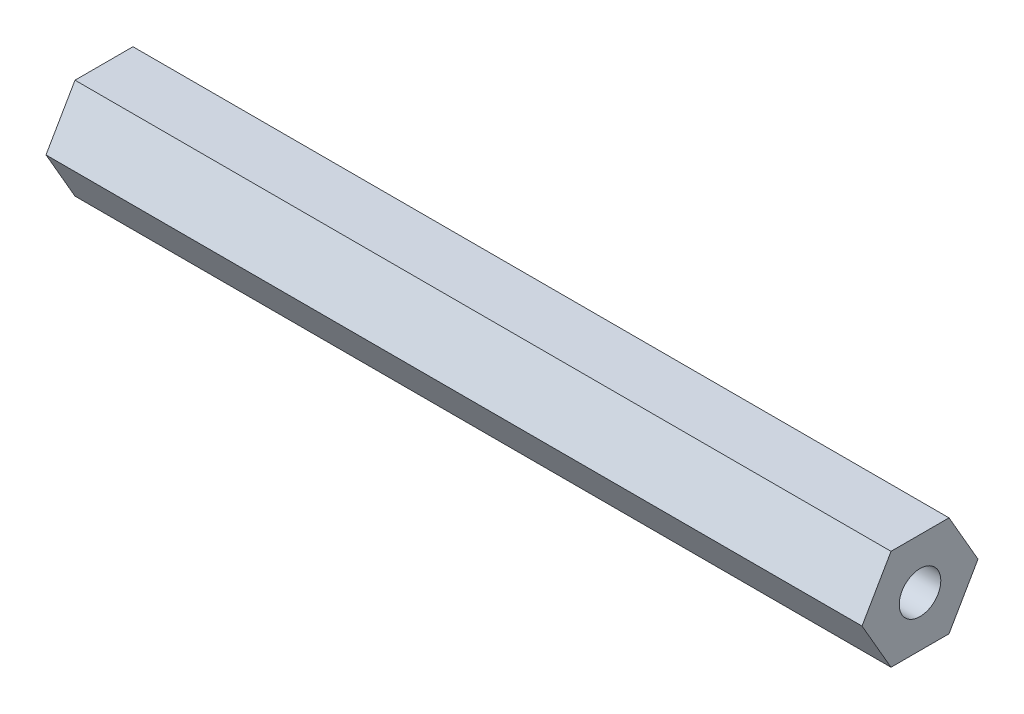
SolidWorks part; units mm, degrees
material "6061-T6 (SS)"
ref_plane "Front Plane" through (0, 0, 0) normal (0, 0, 1) x (1, 0, 0)
ref_plane "Top Plane" through (0, 0, 0) normal (0, 1, 0) x (1, 0, 0)
ref_plane "Right Plane" through (0, 0, 0) normal (1, 0, 0) x (0, 0, -1)
sketch "Sketch1" plane through (0, 0, 0) normal (1, 0, 0) x (0, 0, -1)
  line L1 (3.6662, 6.35) -> (-3.6662, 6.35)
  line L2 (-3.6662, 6.35) -> (-7.3323, 0)
  line L3 (-7.3323, 0) -> (-3.6662, -6.35)
  line L4 (-3.6662, -6.35) -> (3.6662, -6.35)
  line L5 (3.6662, -6.35) -> (7.3323, 0)
  line L6 (7.3323, 0) -> (3.6662, 6.35)
  circle A0 centre (0, 0) radius 6.35 construction
  circle A1 centre (0, 0) radius 2.6289
  dimension "D1" = 12.7
  dimension "D2" = 5.2578
extrude "Boss-Extrude1" add sketch "Sketch1" along normal blind 103.1875
